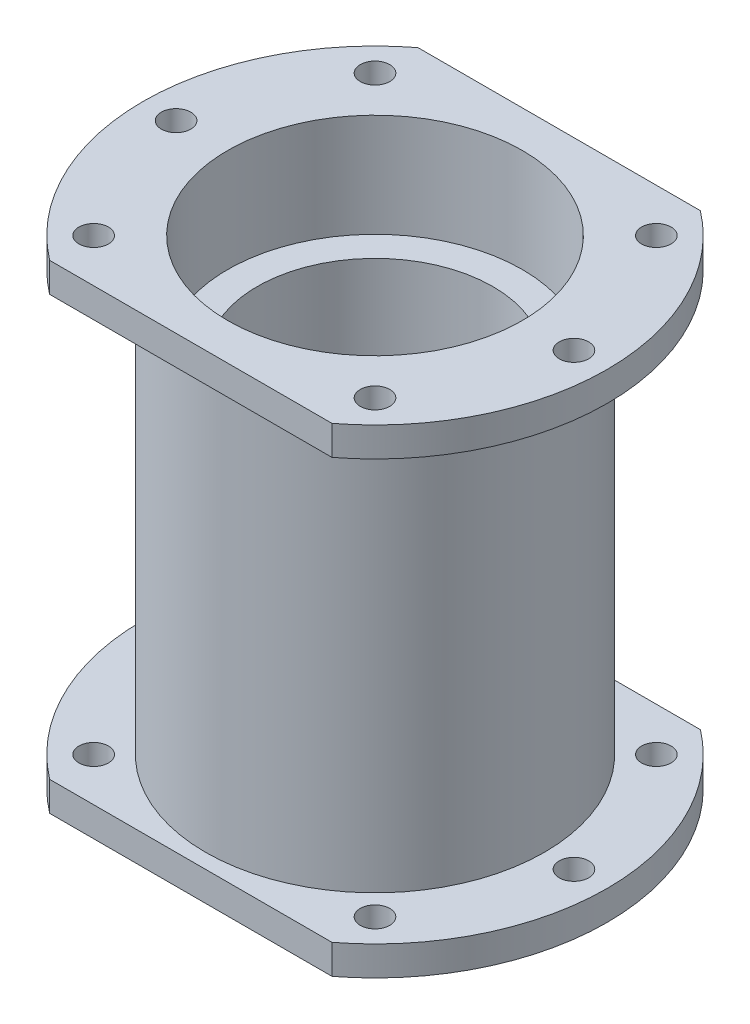
SolidWorks part; units mm, degrees
other "Markup1"
sketch "Sketch3" plane through (21.5, 17.5, -21.5) normal (0.4427, 0.8962, -0.0285) x (0.8481, -0.4288, -0.3112)
material "6061-T4 (SS)"
ref_plane "Front Plane" through (0, 0, 0) normal (0, 0, 1) x (1, 0, 0)
ref_plane "Top Plane" through (0, 0, 0) normal (0, 1, 0) x (1, 0, 0)
ref_plane "Right Plane" through (0, 0, 0) normal (1, 0, 0) x (0, 0, -1)
sketch "Sketch1" plane through (0, 0, 0) normal (0, 0, 1) x (1, 0, 0)
  line L0 (0, 75.0968) -> (0, -85.1516) construction
  line L1 (-12, 2.5) -> (-12, -2.5)
  line L2 (-12, -2.5) -> (-16, -2.5)
  line L3 (-16, -2.5) -> (-16, -18.5)
  line L4 (-16, -18.5) -> (-20, -18.5)
  line L5 (-20, -18.5) -> (-20, -32.5)
  line L13 (-23, 32.5) -> (-23, -32.5)
  line L14 (-12, 0) -> (48.9465, 0) construction
  line L15 (-20, 18.5) -> (-20, 32.5)
  line L16 (-16, 18.5) -> (-20, 18.5)
  line L17 (-16, 2.5) -> (-16, 18.5)
  line L18 (-12, 2.5) -> (-16, 2.5)
  line L19 (-23, 32.5) -> (-20, 32.5)
  line L20 (-23, -32.5) -> (-20, -32.5)
  line L21 (-12, 0) -> (-64.4373, 0) construction
  point P18 (0, 0)
  dimension "D2" = 16
  dimension "D3" = 20
  dimension "D4" = 12
  dimension "D5" = 16
  dimension "D1" = 3
  dimension "D6" = 14
  dimension "D7" = 5
revolve "Revolve1" add sketch "Sketch1" angle 360 about L0
sketch "Sketch4" plane through (0, 32.5, 0) normal (0, 1, 0) x (1, 0, 0)
  circle A0 centre (0, 0) radius 21.5
  circle A1 centre (0, 0) radius 31.5
  circle A2 centre (0, 0) radius 27 construction
  circle A3 centre (0, 27) radius 2
  circle A4 centre (19.0919, 19.0919) radius 2
  circle A5 centre (27, 0) radius 2
  circle A6 centre (19.0919, -19.0919) radius 2
  circle A7 centre (0, -27) radius 2
  circle A8 centre (-19.0919, -19.0919) radius 2
  circle A9 centre (-27, 0) radius 2
  circle A10 centre (-19.0919, 19.0919) radius 2
  point P16 (0, 0)
  dimension "D1" = 43
  dimension "D2" = 10
  dimension "D3" = 54
  dimension "D4" = 4
  dimension "D5" = 8
extrude "Boss-Extrude1" add sketch "Sketch4" against normal blind 4
mirror "Mirror1" about plane through (0, 0, 0) normal (0, 1, 0) of "Boss-Extrude1"
sketch "Sketch5" plane through (0, 32.5, 0) normal (0, 1, 0) x (1, 0, 0)
  line L0 (-45.4714, 0) -> (56.4933, 0) construction
  line L1 (-43.9508, 25) -> (53.2119, 25)
  line L2 (-43.9508, 25) -> (-43.9508, 39.4063)
  line L3 (-43.9508, 39.4063) -> (53.2119, 39.4063)
  line L4 (53.2119, 25) -> (53.2119, 39.4063)
  line L6 (-43.9508, -25) -> (53.2119, -25)
  line L7 (-43.9508, -25) -> (-43.9508, -44.6086)
  line L8 (-43.9508, -44.6086) -> (53.2119, -44.6086)
  line L9 (53.2119, -25) -> (53.2119, -44.6086)
  dimension "D1" = 25
  dimension "D2" = 25
extrude "Cut-Extrude1" cut sketch "Sketch5" against normal through all
